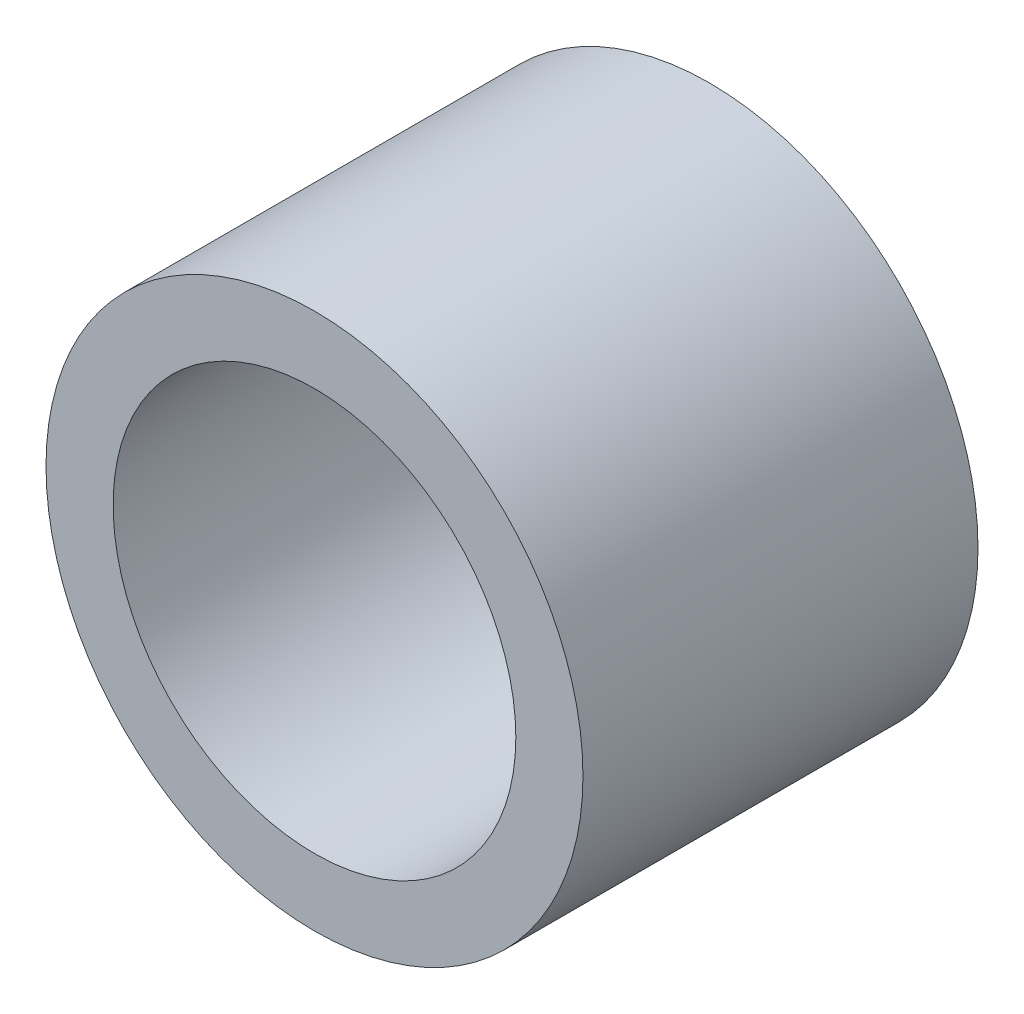
SolidWorks part; units mm, degrees
ref_plane "Front Plane" through (0, 0, 0) normal (0, 0, 1) x (1, 0, 0)
ref_plane "Top Plane" through (0, 0, 0) normal (0, 1, 0) x (1, 0, 0)
ref_plane "Right Plane" through (0, 0, 0) normal (1, 0, 0) x (0, 0, -1)
sketch "Sketch1" plane through (0, 0, 0) normal (0, 0, 1) x (1, 0, 0)
  circle A0 centre (0, 0) radius 7
  circle A1 centre (0, 0) radius 5.25
  dimension "D1" = 14
  dimension "D2" = 10.5
extrude "Boss-Extrude1" add sketch "Sketch1" along normal blind 10.3
